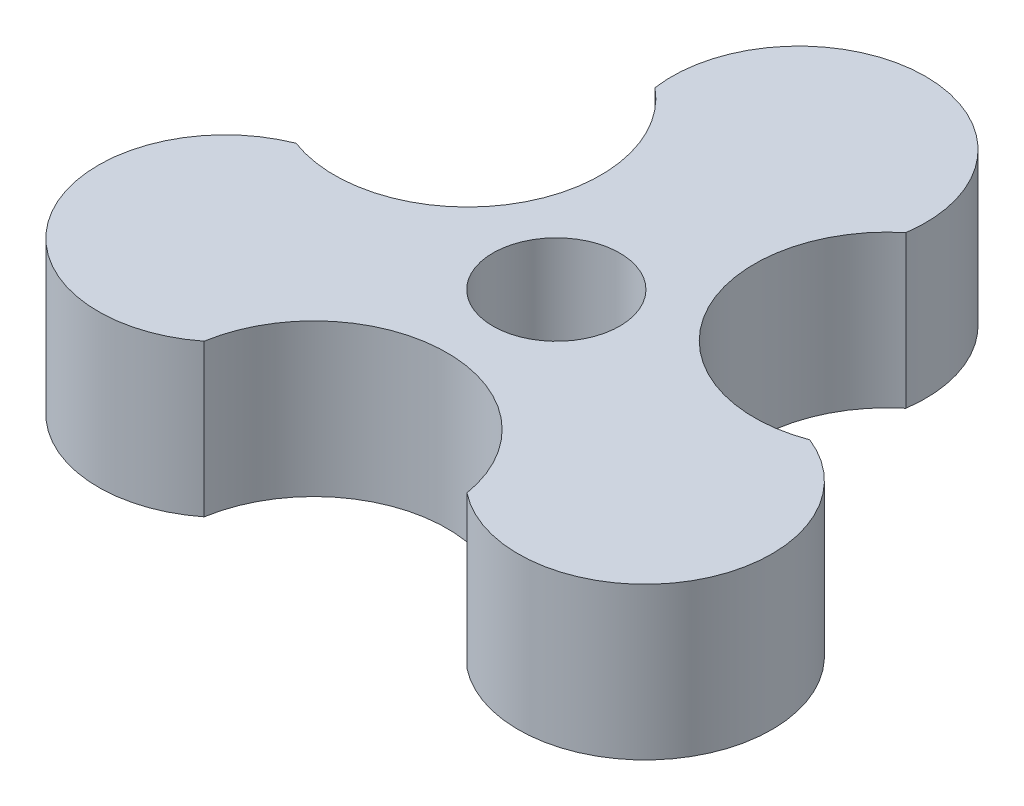
SolidWorks part; units mm, degrees
material "1060 Alloy"
ref_plane "Front" through (0, 0, 0) normal (0, 0, 1) x (1, 0, 0)
ref_plane "Top" through (0, 0, 0) normal (0, 1, 0) x (1, 0, 0)
ref_plane "Right" through (0, 0, 0) normal (1, 0, 0) x (0, 0, -1)
sketch "Sketch2" plane through (0, 0, 0) normal (0, 1, 0) x (1, 0, 0)
  line L21 (0, -55) -> (0, 55) construction
  line L22 (-55, 0) -> (55, 0) construction
  circle A0 centre (0, 0) radius 9.56
  circle A22 centre (0, 9.56) radius 5
  circle A53 centre (8.2792, -4.78) radius 5
  circle A54 centre (-8.2792, -4.78) radius 5
  circle A55 centre (0, -9.56) radius 5.25
  circle A56 centre (-8.2792, 4.78) radius 5.25
  circle A57 centre (8.2792, 4.78) radius 5.25
  point P12 (0, 0)
  point P15 (0, 0)
  point P16 (0, 0)
  point P17 (0, 0)
  point P18 (0, 0)
  point P19 (-0.0135, 0.0234)
  point P20 (0, 0)
  point P21 (0, 0)
  point P26 (0, 0)
  point P28 (0, 0)
  point P30 (0, 0)
  point P32 (0, 0)
  point P33 (0, 0)
  point P41 (0, 0)
  dimension "D1" = 19.12
  dimension "D2" = 10
  dimension "D3" = 3
  dimension "D4" = 10.5
  dimension "D5" = 8.2792
  dimension "D6" = 4.78
  dimension "D7" = 3
  dimension "D8" = 8.2792
  dimension "D9" = 4.78
extrude "Boss-Extrude1" add sketch "Sketch2" along normal blind 6
sketch "Sketch3" plane through (0, 6, 0) normal (0, 1, 0) x (1, 0, 0)
  circle A0 centre (0, 0) radius 2.5
  dimension "D1" = 5
extrude "Cut-Extrude1" cut sketch "Sketch3" against normal blind 8
